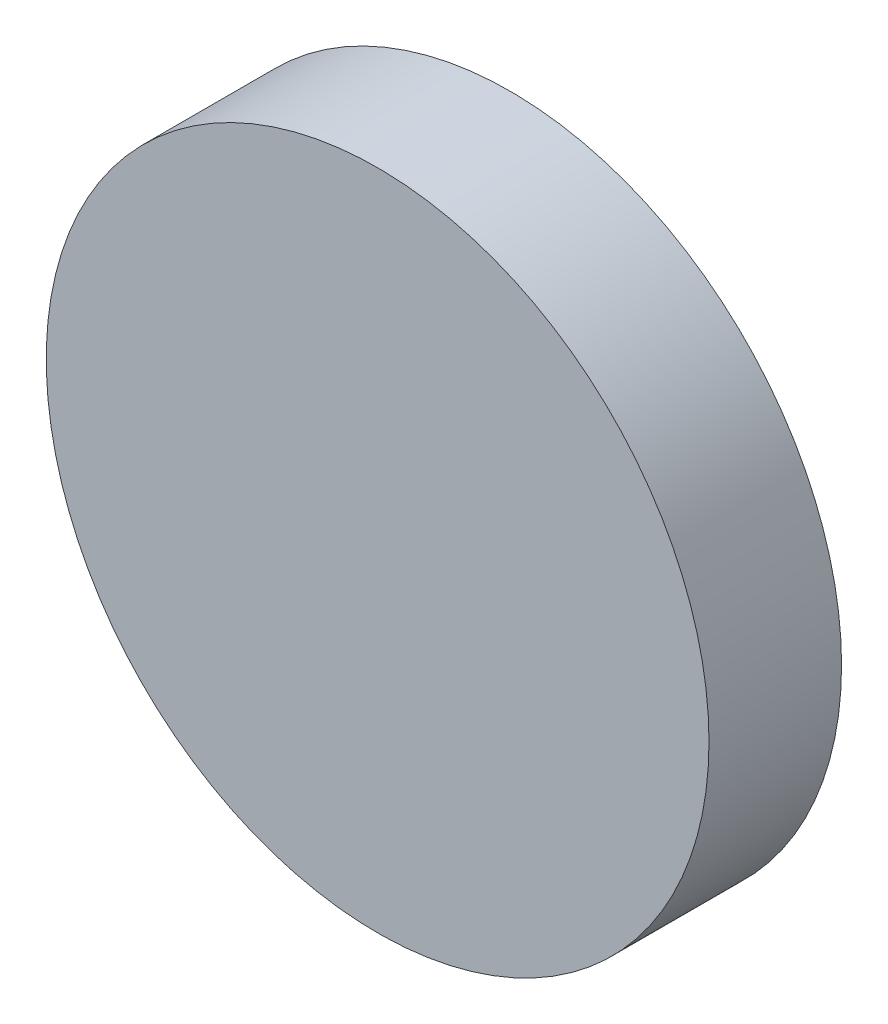
SolidWorks part; units mm, degrees
ref_plane "前视基准面" through (0, 0, 0) normal (0, 0, 1) x (1, 0, 0)
ref_plane "上视基准面" through (0, 0, 0) normal (0, 1, 0) x (1, 0, 0)
ref_plane "右视基准面" through (0, 0, 0) normal (1, 0, 0) x (0, 0, -1)
sketch "草图1" plane through (0, 0, 0) normal (0, 0, 1) x (1, 0, 0)
  circle A0 centre (0, 0) radius 5
  dimension "D1" = 10
extrude "凸台-拉伸1" add sketch "草图1" along normal blind 2 contours A0
